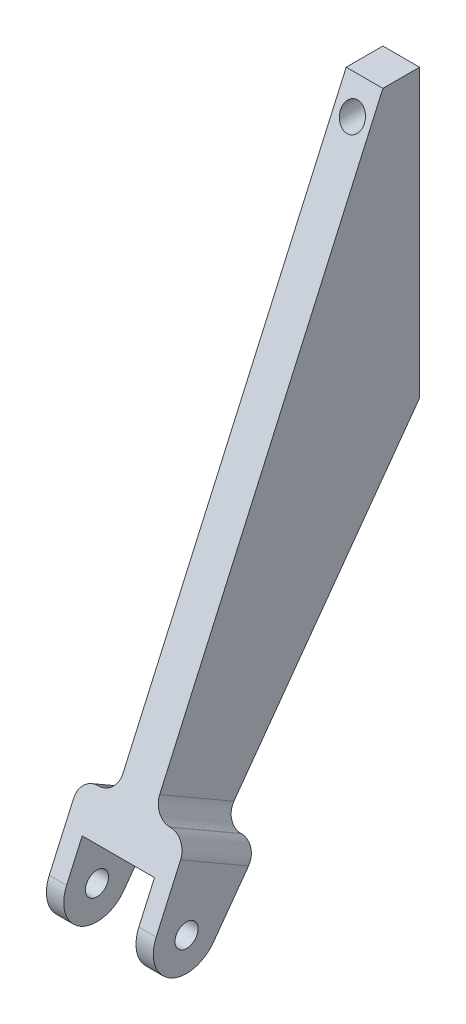
SolidWorks part; units mm, degrees
ref_plane "Front Plane" through (0, 0, 0) normal (0, 0, 1) x (1, 0, 0)
ref_plane "Top Plane" through (0, 0, 0) normal (0, 1, 0) x (1, 0, 0)
ref_plane "Right Plane" through (0, 0, 0) normal (1, 0, 0) x (0, 0, -1)
sketch "Sketch1" plane through (0, 0, 0) normal (0, 0, 1) x (1, 0, 0)
  line L1 (-72.0584, -12.4142) -> (-72.0584, -329.7013) construction
  line L4 (-78.4084, -322.2124) -> (-65.7084, -322.2124)
  line L5 (-78.4084, -322.2124) -> (-78.4084, -2.8892)
  line L6 (-78.4084, -2.8892) -> (-65.7084, -2.8892)
  line L7 (-65.7084, -322.2124) -> (-65.7084, -2.8892)
  line L8 (-78.4084, -322.2124) -> (-65.7084, -2.8892) construction
  line L9 (-78.4084, -2.8892) -> (-65.7084, -322.2124) construction
  point P0 (-72.0584, -162.5508)
  dimension "D1" = 12.7
extrude "Boss-Extrude1" add sketch "Sketch1" along normal blind 112.776
sketch "Sketch2" plane through (-65.7084, 0, 0) normal (1, 0, 0) x (0, 0, -1)
  line L0 (0, -102) -> (-83.4596, -217.2296)
  line L1 (0, -322.2124) -> (0, -2.8892) construction
  line L2 (0, -2.8892) -> (-12.7, -2.8892)
  line L3 (-112.776, -2.8892) -> (0, -2.8892) construction
  line L4 (19.05, -102) -> (0, -102) construction
  line L5 (-12.7, -2.8892) -> (-103.2746, -205.7962)
  line L6 (0, -102) -> (0, -2.8892)
  line L8 (-143.9151, -343.6077) -> (30.3223, -343.6077)
  line L9 (-143.9151, -343.6077) -> (-143.9151, 9.7561)
  line L10 (-143.9151, 9.7561) -> (30.3223, 9.7561)
  line L11 (30.3223, -343.6077) -> (30.3223, 9.7561)
  circle A0 centre (9.525, -112) radius 142 construction
  circle A5 centre (9.525, -112) radius 142 construction
  arc A6 (-103.2746, -205.7962) -> (-83.4596, -217.2296) centre (-92.7733, -210.4838) ccw
  circle A7 centre (-92.7733, -210.4838) radius 4
  dimension "D4" = 23
  dimension "D5" = 8
  dimension "D1" = 12.7
extrude "Cut-Extrude1" cut sketch "Sketch2" against normal through all
sketch "Sketch3" plane through (0, 0, 0) normal (0, 0, -1) x (-1, 0, 0)
  line L0 (72, -12.4142) -> (72, -91.7892) construction
  circle A0 centre (72, -12.4142) radius 4.1275
  circle A1 centre (72, -91.7892) radius 4.1275
  dimension "D1" = 79.375
  dimension "D2" = 8.255
extrude "Cut-Extrude2" cut sketch "Sketch3" against normal blind 25.4
ref_plane "Plane1" through (-72.0584, 0, 0) normal (1, 0, 0) x (0, 0, -1)
sketch "Sketch4" plane through (-72.0584, 0, 0) normal (1, 0, 0) x (0, 0, -1)
  line L1 (-12.7, -2.8892) -> (-103.2746, -205.7962) construction
  line L5 (-67.7794, -195.5804) -> (-92.3785, -181.3865)
  line L6 (0, -102) -> (-83.4596, -217.2296) construction
  line L8 (-92.7733, -210.4838) -> (-80.0789, -188.4835) construction
  line L10 (-83.4596, -217.2296) -> (-67.7794, -195.5804)
  line L11 (-103.2746, -205.7962) -> (-92.3785, -181.3865)
  circle A2 centre (-92.7733, -210.4838) radius 4 construction
  circle A3 centre (-92.7733, -210.4838) radius 4
  arc A4 (-103.2746, -205.7962) -> (-83.4596, -217.2296) centre (-92.7733, -210.4838) ccw construction
  arc A5 (-103.2746, -205.7962) -> (-83.4596, -217.2296) centre (-92.7733, -210.4838) ccw
  dimension "D2" = 25.4
extrude "Boss-Extrude2" add sketch "Sketch4" along normal mid plane 37
sketch "Sketch6" plane through (-72.0584, 0, 0) normal (1, 0, 0) x (0, 0, -1)
  line L0 (-102.8827, -190.7962) -> (-56.5696, -217.5193)
  line L1 (-56.5696, -217.5193) -> (-85.0862, -269.6791)
  line L2 (-85.0862, -269.6791) -> (-153.8338, -230.3279)
  line L3 (-153.8338, -230.3279) -> (-102.8827, -190.7962)
  line L5 (-67.7794, -195.5804) -> (-92.3785, -181.3865) construction
  circle A0 centre (-92.7733, -210.4838) radius 4 construction
  circle A1 centre (-92.7733, -210.4838) radius 4 construction
  dimension "D1" = 12
extrude "Cut-Extrude3" cut sketch "Sketch6" against normal mid plane 25
fillet "Fillet1" radius 6 4 edges at (-90.5584, -188.4835, 80.0789) (-78.4084, -188.4835, 80.0789) (-53.5584, -188.4835, 80.0789) (-65.7084, -188.4835, 80.0789)
